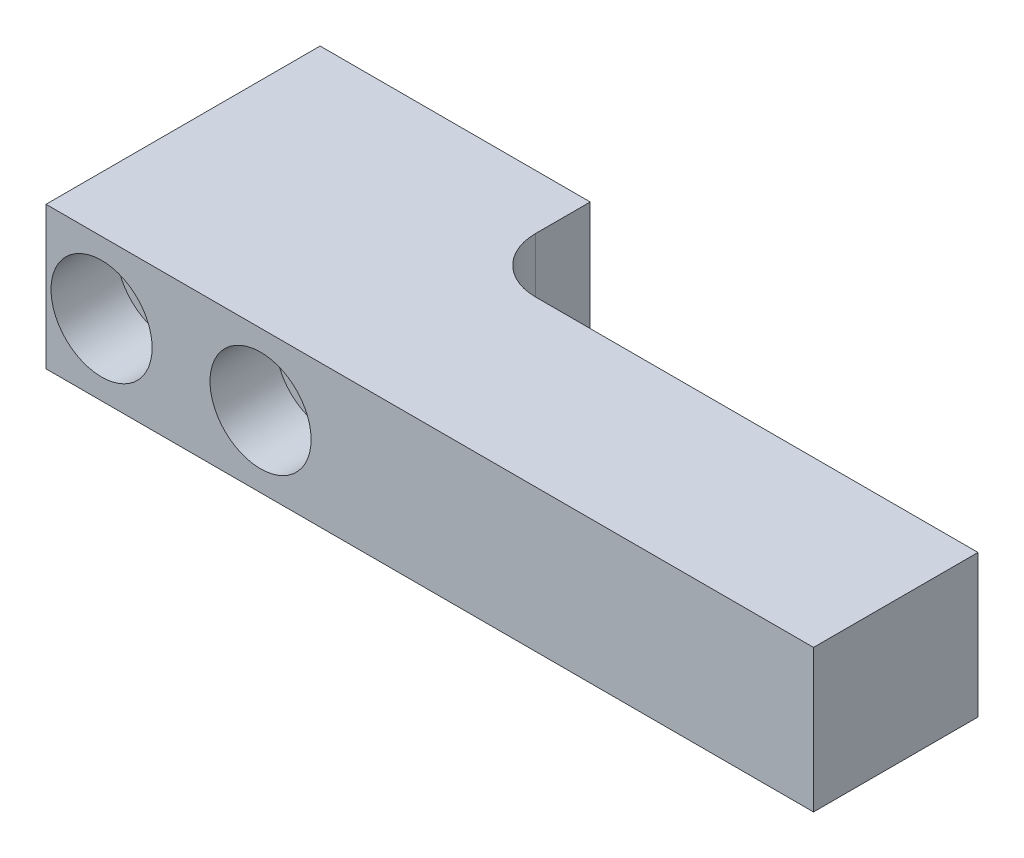
SolidWorks part; units mm, degrees
ref_plane "Front Plane" through (0, 0, 0) normal (0, 0, 1) x (1, 0, 0)
ref_plane "Top Plane" through (0, 0, 0) normal (0, 1, 0) x (1, 0, 0)
ref_plane "Right Plane" through (0, 0, 0) normal (1, 0, 0) x (0, 0, -1)
sketch "Sketch1" plane through (0, 0, 0) normal (0, 0, 1) x (1, 0, 0)
  line L0 (0, 0) -> (80, 0) construction
  line L1 (0, 13) -> (24.634, 13)
  line L2 (0, 13) -> (0, 0)
  line L3 (0, 0) -> (24.634, 0)
  line L4 (24.634, 13) -> (24.634, 0)
  line L5 (5.067, 6.5) -> (0, 6.5) construction
  line L6 (24.634, 6.5) -> (19.567, 6.5) construction
extrude "Boss-Extrude1" add sketch "Sketch1" along normal blind 10
sketch "Sketch4" plane through (0, 0, 10) normal (0, 0, 1) x (1, 0, 0)
  line L0 (24.634, 13) -> (0, 13) construction
  line L1 (0, 0) -> (70, 0)
  line L2 (0, 0) -> (0, 13)
  line L3 (0, 13) -> (70, 13)
  line L4 (70, 0) -> (70, 13)
  line L5 (80, 0) -> (80, 13) construction
  dimension "D1" = 10
extrude "Boss-Extrude4" add sketch "Sketch4" along normal blind 15
fillet "Fillet2" radius 5 1 edges at (24.634, 6.5, 10)
sketch "Sketch11" plane through (0, 0, 0) normal (0, 0, -1) x (-1, 0, 0)
  line L0 (0, 6.5) -> (-24.634, 6.5) construction
  line L1 (0, 13) -> (0, 0) construction
  line L2 (-24.634, 0) -> (-24.634, 13) construction
  circle A0 centre (-5.067, 6.5) radius 2.68
  circle A1 centre (-19.567, 6.5) radius 2.68
  dimension "D3" = 5.36
  dimension "D4" = 5.36
  dimension "D1" = 5.067
  dimension "D2" = 14.5
extrude "Cut-Extrude3" cut sketch "Sketch11" against normal through all
sketch "Sketch12" plane through (0, 0, 25) normal (0, 0, 1) x (1, 0, 0)
  circle A0 centre (5.067, 6.5) radius 4.61
  circle A1 centre (19.567, 6.5) radius 4.61
  dimension "D1" = 9.22
  dimension "D2" = 9.22
extrude "Cut-Extrude4" cut sketch "Sketch12" against normal blind 6
